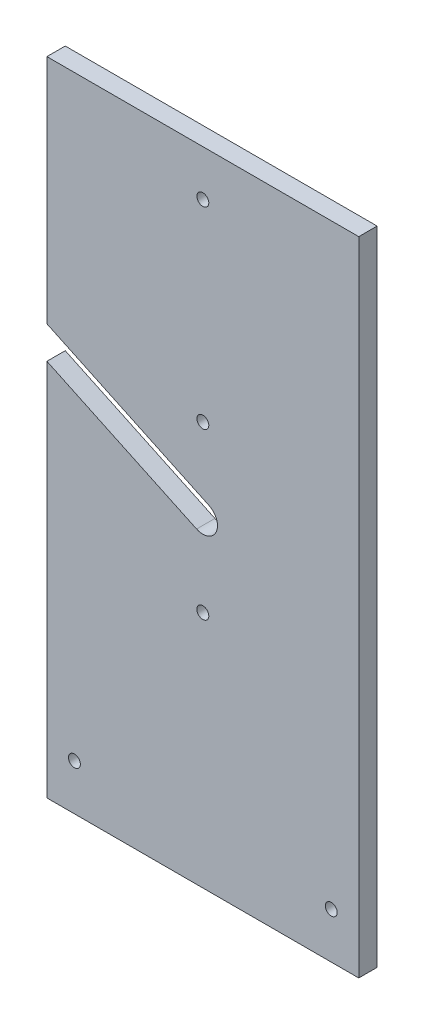
SolidWorks part; units mm, degrees
ref_plane "Ebene vorne" through (0, 0, 0) normal (0, 0, 1) x (1, 0, 0)
ref_plane "Ebene oben" through (0, 0, 0) normal (0, 1, 0) x (1, 0, 0)
ref_plane "Ebene rechts" through (0, 0, 0) normal (1, 0, 0) x (0, 0, -1)
sketch "Skizze1" plane through (0, 0, 0) normal (0, 0, 1) x (1, 0, 0)
  line L11 (0, 0) -> (-85, 40) construction
  line L27 (85, 175) -> (-85, 175)
  line L28 (85, 175) -> (85, -175)
  line L29 (85, -175) -> (-85, -175)
  line L30 (-85, 175) -> (-85, 48.8416)
  line L31 (85, 175) -> (-85, -175) construction
  line L32 (85, -175) -> (-85, 175) construction
  line L33 (-3.4064, -7.2385) -> (-85, 31.1584)
  line L36 (3.4064, 7.2385) -> (-85, 48.8416)
  line L37 (-85, 31.1584) -> (-85, -175)
  arc A6 (-3.4064, -7.2385) -> (3.4064, 7.2385) centre (0, 0) ccw
  point P0 (0, 0)
  point P7 (-43.367, 12.2952)
  point P10 (50, 0)
  point P11 (-70, -150)
  point P12 (50, 240)
  point P16 (-25, -43.3013)
  point P17 (182.8461, -163.3013)
  point P18 (-25, 43.3013)
  point P20 (-232.8461, -76.6987)
  point P21 (-50, 0)
  point P22 (-50, 240)
  point P23 (25, 43.3013)
  point P24 (232.8461, -76.6987)
  point P25 (25, -43.3013)
  point P26 (-182.8461, -163.3013)
  point P29 (70, -150)
  point P30 (0, 150)
  point P32 (0, 175)
  dimension "D3" = 350
  dimension "D8" = 15
  dimension "D1" = 8
  dimension "D2" = 170
  dimension "D4" = 25
  dimension "D5" = 25
  dimension "D6" = 25
  dimension "D7" = 40
  dimension "D9" = 15
  dimension "D10" = 8
  dimension "D11" = 8
extrude "Aufsatz-Linear austragen1" add sketch "Skizze1" along normal blind 10
hole_wizard "Ø6.5 (6.5) Durchmesser Bohrung5" positions "Skizze19" profile "Skizze18" hole size "Ø6.5" standard "ISO" end condition through all
sketch "Skizze19" plane through (0, 0, 10) normal (0, 0, 1) x (1, 0, 0)
  point P0 (0, 150)
  point P3 (-70, -150)
  point P6 (70, -150)
  point P9 (0, 45)
  point P11 (0, -45)
  dimension "D1" = 45
  dimension "D2" = 45
sketch "Skizze18" plane through (0, 150, 10) normal (1, 0, 0) x (0, -1, 0)
  line L0 (0, 0) -> (0, 10)
  line L1 (0, 10) -> (3.25, 10)
  line L2 (3.25, 10) -> (3.25, 0)
  line L5 (3.25, 0) -> (0, 0)
  line L11 (0, -6.35) -> (0, 107.95) construction
  dimension "Bohrerdurchmesser" = 6.5
  dimension "Bohrungstiefe" = 10
